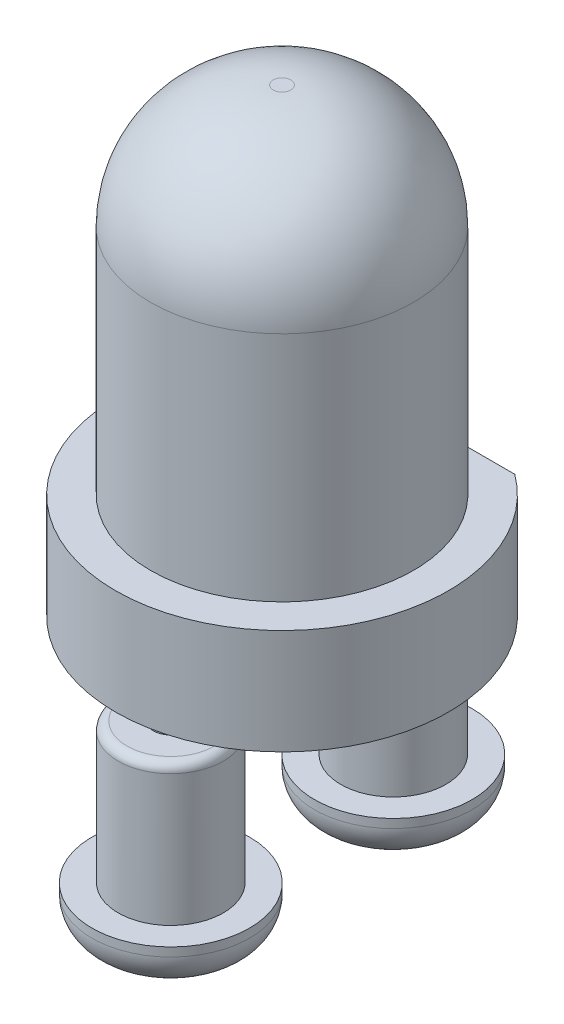
SolidWorks part; units mm, degrees
material "ABS"
ref_plane "Front Plane" through (0, 0, 0) normal (0, 0, 1) x (1, 0, 0)
ref_plane "Top Plane" through (0, 0, 0) normal (0, 1, 0) x (1, 0, 0)
ref_plane "Right Plane" through (0, 0, 0) normal (1, 0, 0) x (0, 0, -1)
sketch "Sketch1" plane through (0, 0, 0) normal (0, 0, 1) x (1, 0, 0)
  line L0 (0, 0) -> (0, 5.25)
  line L1 (0, 0) -> (1.9, 0)
  line L2 (1.9, 0) -> (1.9, 1.2)
  line L3 (1.9, 1.2) -> (1.5, 1.2)
  line L4 (1.5, 1.2) -> (1.5, 3.85)
  line L5 (1.5, 3.85) -> (1.5, 5.25) construction
  line L6 (1.5, 5.25) -> (0.1, 5.25) construction
  line L7 (0.1, 5.25) -> (0, 5.25)
  arc A0 (0.1, 5.25) -> (1.5, 3.85) centre (0.1, 3.85) cw
  dimension "D5" = 1.4
  dimension "D1" = 5.25
  dimension "D2" = 1.2
  dimension "D3" = 1.9
  dimension "D4" = 1.5
revolve "Revolve1" add sketch "Sketch1" angle 360 about L0
sketch "Sketch2" plane through (0, 1.2, 0) normal (0, 1, 0) x (1, 0, 0)
  line L0 (0, 0) -> (0, 1.53) construction
  line L2 (-1.5, 2.03) -> (1.5, 2.03)
  line L3 (-1.5, 2.03) -> (-1.5, 1.53)
  line L4 (-1.5, 1.53) -> (1.5, 1.53)
  line L5 (1.5, 2.03) -> (1.5, 1.53)
  dimension "D1" = 3
  dimension "D2" = 0.5
  dimension "D3" = 1.53
extrude "Cut-Extrude1" cut sketch "Sketch2" against normal up to surface (1.2 mm away) up to face at (0, 0, -1.9)
sketch "Sketch3" plane through (0, 0, 0) normal (0, -1, 0) x (1, 0, 0)
  line L0 (0, 1.27) -> (0, -1.27) construction
  circle A0 centre (0, 1.27) radius 0.2
  circle A1 centre (0, -1.27) radius 0.2
  dimension "D2" = 0.4
  dimension "D1" = 2.54
extrude "Boss-Extrude1" add sketch "Sketch3" along normal blind 17.5
sketch "Sketch4" plane through (0, -17.5, 0) normal (0, -1, 0) x (1, 0, 0)
  circle A1 centre (0, 1.27) radius 0.2
  circle A2 centre (0, 1.27) radius 0.2
  dimension "D1" = 0
extrude "Boss-Extrude2" add sketch "Sketch4" along normal blind 1.5
sketch "Sketch5" plane through (0, 0, 0) normal (1, 0, 0) x (0, 0, -1)
  line L0 (-1.47, -19) -> (-1.07, -19) construction
  line L1 (-2.5, -2) -> (2.5, -2)
  line L2 (-2.5, -2) -> (-2.5, -19)
  line L3 (-2.5, -19) -> (2.5, -19)
  line L4 (2.5, -2) -> (2.5, -19)
  dimension "D1" = 2
  dimension "D2" = 2.5
  dimension "D3" = 5
extrude "Cut-Extrude2" cut sketch "Sketch5" against normal through all both and the other way through all
sketch "Sketch6" plane through (0, -2, 0) normal (0, -1, 0) x (1, 0, 0)
  circle A0 centre (0, 1.27) radius 0.9
  circle A1 centre (0, -1.27) radius 0.9
  dimension "D1" = 1.8
extrude "Boss-Extrude3" add sketch "Sketch6" along normal blind 0.5
fillet "Fillet2" radius 0.4 2 edges at (0, -2.5, -2.17) (0, -2.5, 0.37)
sketch "Sketch7" plane through (0, -2, 0) normal (0, 1, 0) x (1, 0, 0)
  circle A0 centre (0, -1.27) radius 0.6
  circle A1 centre (0, 1.27) radius 0.6
  dimension "D1" = 1.2
extrude "Boss-Extrude4" add sketch "Sketch7" along normal blind 1.6
fillet "Fillet3" radius 0.1 2 edges at (0, -0.4, -0.67) (0, -0.4, 1.87)
